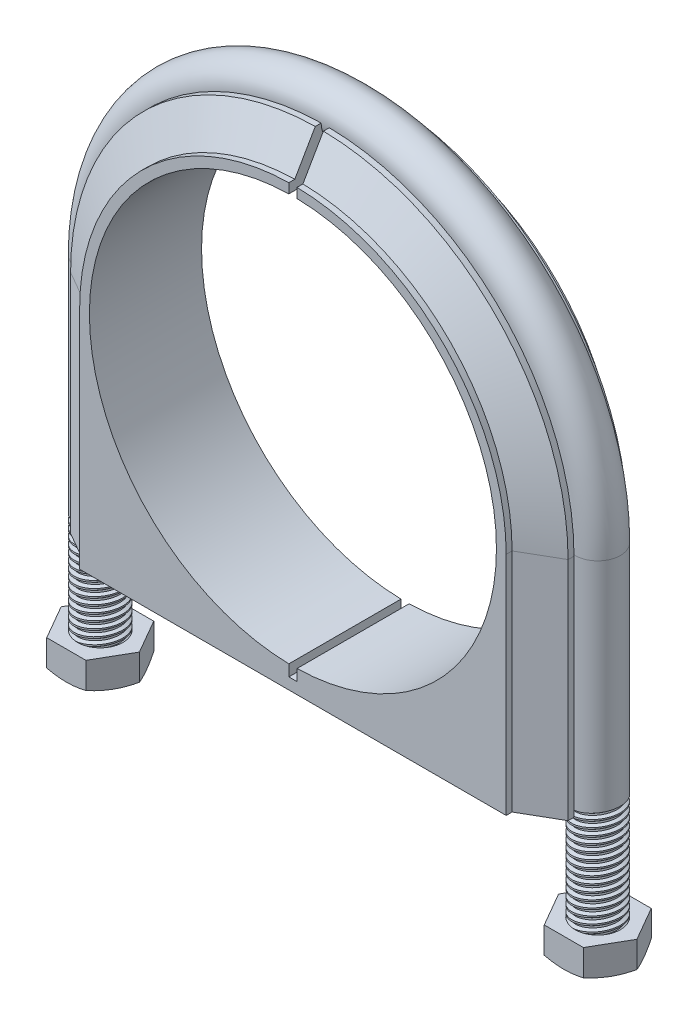
SolidWorks part; units mm, degrees
ref_plane "Front" through (0, 0, 0) normal (0, 0, 1) x (1, 0, 0)
ref_plane "Top" through (0, 0, 0) normal (0, 1, 0) x (1, 0, 0)
ref_plane "Right" through (0, 0, 0) normal (1, 0, 0) x (0, 0, -1)
sketch "Sketch1" plane through (0, 0, 0) normal (0, 0, 1) x (1, 0, 0)
  line L0 (-63.5, 0) -> (-63.5, 99.06)
  line L1 (63.5, 99.06) -> (63.5, 0)
  line L2 (-63.5, 0) -> (63.5, 0) construction
  line L3 (0, 0) -> (0, 99.06) construction
  line L4 (-69.85, 0) -> (-69.85, 99.06) construction
  line L5 (69.85, 99.06) -> (69.85, 0) construction
  line L6 (-63.5, 0) -> (-76.2, 0) construction
  line L7 (-76.2, 0) -> (-76.2, 99.06) construction
  arc A0 (-63.5, 99.06) -> (63.5, 99.06) centre (0, 99.06) cw
  arc A1 (-69.85, 99.06) -> (69.85, 99.06) centre (0, 99.06) cw construction
  dimension "ID" = 127
  dimension "Wire Dia" = 12.7
  dimension "C-C" = 139.7
  dimension "D" = 99.06
sketch "Sketch2" plane through (0, 0, 0) normal (0, 1, 0) x (1, 0, 0)
  line L0 (-63.5, 0) -> (-76.2, 0) construction
  circle A0 centre (-69.85, 0) radius 6.35
sweep "Sweep1" add profiles "Sketch2" path "Sketch1"
sketch "Sketch4" plane through (0, 0, 0) normal (0, 0, 1) x (1, 0, 0)
  line L0 (-76.2, 38.1) -> (-63.5, 38.1) construction
  line L1 (-63.5, 38.1) -> (-76.2, 36.1462) construction
  line L2 (-76.2, 36.1462) -> (-76.2, 38.1) construction
  line L3 (-63.5, 38.1) -> (-64.4524, 37.3357)
  line L4 (-64.4524, 37.3357) -> (-64.3781, 36.8529)
  line L5 (-64.3781, 36.8529) -> (-63.24, 36.4103)
  line L6 (-63.24, 36.4103) -> (-63.5, 38.1)
  line L7 (-63.24, 36.4103) -> (-63.2029, 36.1689) construction
  line L8 (-64.4153, 37.0943) -> (-63.37, 37.2551) construction
  line L9 (-76.2, 0) -> (-76.2, 99.06) construction
  line L15 (-63.5, 0) -> (-63.5, 99.06) construction
  line L16 (-63.5, 37.2351) -> (-76.2, 35.2813) construction
  line L17 (-69.5666, 34.4164) -> (-70.1334, 38.1) construction
  line L18 (-63.5, 0) -> (-76.2, 0) construction
  point P17 (-69.85, 36.2582)
  dimension "D1" = 60
  dimension "D2" = 0.2442
  dimension "D3" = 0.4885
  dimension "Thread Pitch" = 1.9538
  dimension "D4" = 1.9538
  dimension "Thread Length" = 38.1
revolve "Cut-Revolve1" cut sketch "Sketch4" angle 360 about L17
sketch "Sketch5" plane through (0, 0, 0) normal (0, 0, 1) x (1, 0, 0)
  line L0 (-63.5, 0) -> (-63.5, 2.0425)
  line L1 (-63.5, 2.0425) -> (-64.4524, 0)
  line L2 (-64.4524, 0) -> (-63.5, 0)
  line L3 (-63.5, 0) -> (-76.2, 0) construction
  line L4 (-63.5, 0) -> (-63.5, 99.06) construction
  line L5 (-69.85, -0.74) -> (-69.85, 2.2885) construction
  line L6 (-69.85, 0) -> (-69.85, 99.06) construction
  line L7 (63.5, 2.0425) -> (63.5, 0) construction
  line L8 (63.5, 0) -> (64.4524, 0) construction
  line L9 (64.4524, 0) -> (63.5, 2.0425) construction
  line L10 (63.5, 99.06) -> (63.5, 0) construction
  dimension "D1" = 25
revolve "Cut-Revolve2" cut sketch "Sketch5" angle 360 about L5
sketch "Sketch6" plane through (0, 0, 0) normal (0, 0, 1) x (1, 0, 0)
  line L0 (63.5, 0) -> (64.4524, 0) construction
  line L1 (64.4524, 0) -> (63.5, 2.0425) construction
  line L2 (63.5, 2.0425) -> (63.5, 0) construction
  line L3 (63.5, 0) -> (64.4524, 0)
  line L4 (64.4524, 0) -> (63.5, 2.0425)
  line L5 (63.5, 2.0425) -> (63.5, 0)
  line L6 (69.85, 2.7026) -> (69.85, -1.5063) construction
  line L7 (69.85, 99.06) -> (69.85, 0) construction
revolve "Cut-Revolve3" cut sketch "Sketch6" angle 360 about L6
pattern_linear "LPattern2" count 2 spacing 139.7 along (1, 0, 0) count 19 spacing 1.9538 along (0, -1, 0) of "Cut-Revolve1"
sketch "Sketch9" plane through (0, 0, 0) normal (0, 0, 1) x (1, 0, 0)
  line L0 (-63.5, 0) -> (63.5, 0) construction
  line L1 (0, 0) -> (0, 99.06) construction
  line L2 (63.5, 99.06) -> (63.5, 0) construction
  line L3 (-63.5, 0) -> (-63.5, 99.06) construction
  line L4 (-63.5, 0) -> (63.5, 0) construction
  line L5 (0, 0) -> (0, 99.06) construction
  line L6 (63.5, 99.06) -> (63.5, 35.56)
  line L7 (-63.5, 35.56) -> (-63.5, 99.06)
  line L8 (-63.5, 35.56) -> (63.5, 35.56) construction
  arc A0 (63.5, 99.06) -> (-63.5, 99.06) centre (0, 99.06) ccw construction
  arc A1 (63.5, 99.06) -> (-63.5, 99.06) centre (0, 99.06) ccw
  dimension "E" = 63.5
ref_plane "Plane2" through (0, 35.56, 0) normal (0, 1, 0) x (-1, 0, 0)
sketch "Sketch10" plane through (0, 35.56, 0) normal (0, 1, 0) x (-1, 0, 0)
  line L0 (69.85, 6.6675) -> (69.85, 8.3303)
  line L1 (69.85, 8.3303) -> (59.8823, 14.0852)
  line L2 (59.8823, 14.0852) -> (59.8823, 15.748)
  line L3 (59.8823, 15.748) -> (3.175, 15.748)
  line L4 (3.175, 15.748) -> (3.175, -15.748)
  line L5 (3.175, -15.748) -> (59.8823, -15.748)
  line L6 (59.8823, -15.748) -> (59.8823, -14.0852)
  line L7 (59.8823, -14.0852) -> (69.85, -8.3303)
  line L8 (69.85, -8.3303) -> (69.85, -6.6675)
  line L9 (76.2, 0) -> (63.5, 0) construction
  line L10 (57.15, 15.748) -> (57.15, -15.748) construction
  line L11 (0, 0) -> (0, -15.748) construction
  circle A0 centre (69.85, 0) radius 6.35 construction
  circle A1 centre (69.85, 0) radius 6.35 construction
  arc A2 (69.85, 6.6675) -> (69.85, -6.6675) centre (69.85, 0) ccw
  dimension "D1" = 12.7
  dimension "D2" = 13.335
  dimension "D3" = 30
  dimension "D4" = 3.175
  dimension "D5" = 12.7
  dimension "F" = 31.496
  dimension "A Hole" = 114.3
  dimension "D6" = 2.7323
sweep "Sweep2" add profiles "Sketch10" path "Sketch9"
sketch "Sketch11" plane through (0, 0, 0) normal (0, 0, 1) x (1, 0, 0)
  line L0 (3.175, 35.56) -> (-3.175, 35.56)
  line L6 (-59.8823, 35.56) -> (-3.175, 35.56)
  line L7 (-59.8823, 99.06) -> (-59.8823, 35.56)
  line L8 (59.8823, 35.56) -> (59.8823, 99.06)
  line L10 (3.175, 99.06) -> (3.175, 35.56)
  line L11 (-3.175, 35.56) -> (-3.175, 99.06)
  line L13 (3.175, 35.56) -> (59.8823, 35.56)
  line L16 (3.175, 99.06) -> (3.175, 35.56)
  line L17 (-3.175, 35.56) -> (-3.175, 99.06)
  arc A2 (59.8823, 99.06) -> (-59.8823, 99.06) centre (0, 99.06) ccw
  arc A3 (3.175, 99.06) -> (-3.175, 99.06) centre (0, 99.06) ccw
  arc A5 (3.175, 99.06) -> (-3.175, 99.06) centre (0, 99.06) ccw
  dimension "D1" = 0
extrude "Extrude2" add sketch "Sketch11" against normal up to surface (15.748 mm away) and the other way up to surface (15.748 mm away)
sketch "Sketch12" plane through (0, 0, 0) normal (0, 0, 1) x (1, 0, 0)
  line L0 (-57.15, 99.06) -> (57.15, 99.06) construction
  line L1 (0, 99.06) -> (0, 168.91) construction
  line L2 (-1.143, 168.91) -> (1.143, 168.91)
  line L3 (-1.143, 168.91) -> (-1.143, 156.1986)
  line L4 (-1.143, 41.9214) -> (-1.143, 38.7407)
  line L5 (1.143, 168.91) -> (1.143, 156.1986)
  line L6 (-1.143, 38.7407) -> (1.143, 38.7407)
  line L7 (1.143, 38.7407) -> (1.143, 41.9214)
  line L8 (0, 38.7407) -> (0, 35.56) construction
  arc A0 (-1.143, 156.1986) -> (-1.143, 41.9214) centre (0, 99.06) ccw
  arc A1 (63.5, 99.06) -> (-63.5, 99.06) centre (0, 99.06) ccw construction
  arc A2 (69.85, 99.06) -> (-69.85, 99.06) centre (0, 99.06) ccw construction
  arc A3 (1.143, 41.9214) -> (1.143, 156.1986) centre (0, 99.06) ccw
  dimension "D1" = 114.3
  dimension "D2" = 2.286
extrude "Cut-Extrude1" cut sketch "Sketch12" against normal through all and the other way through all
ref_plane "Plane1" through (0, 34.798, 0) normal (0, -1, 0) x (1, 0, 0)
sketch "Sketch7" plane through (0, 34.798, 0) normal (0, -1, 0) x (1, 0, 0)
  line L1 (-58.8515, 0) -> (-64.3507, 9.525)
  line L2 (-64.3507, 9.525) -> (-75.3493, 9.525)
  line L3 (-75.3493, 9.525) -> (-80.8485, 0)
  line L4 (-80.8485, 0) -> (-75.3493, -9.525)
  line L5 (-75.3493, -9.525) -> (-64.3507, -9.525)
  line L6 (-64.3507, -9.525) -> (-58.8515, 0)
  circle A0 centre (-69.85, 0) radius 6.36
  circle A1 centre (-69.85, 0) radius 9.525 construction
  dimension "D1" = 12.72
  dimension "Nut Width" = 19.05
extrude "Extrude1" add sketch "Sketch7" along normal up to surface (34.798 mm away) separate body up to face at (-69.85, 0, -5.3976)
sketch "Sketch8" plane through (0, 0, 0) normal (0, 0, 1) x (1, 0, 0)
  line L0 (-60.325, 34.798) -> (-58.8515, 34.1109)
  line L1 (-58.8515, 34.1109) -> (-58.8515, 0.6871) construction
  line L2 (-58.8515, 0.6871) -> (-60.325, 0)
  line L3 (-60.325, 0) -> (-80.8485, 0) construction
  line L4 (-80.8485, 0) -> (-80.8485, 34.798) construction
  line L5 (-80.8485, 34.798) -> (-60.325, 34.798) construction
  line L6 (-75.3493, 34.798) -> (-80.8485, 34.798) construction
  line L7 (-75.3493, 0) -> (-80.8485, 0) construction
  line L8 (-69.85, 13.5515) -> (-69.85, 10.9005) construction
  line L9 (-58.8515, 0) -> (-58.8515, 34.798) construction
  line L10 (-60.325, 34.798) -> (-58.8515, 34.798)
  line L11 (-69.85, 0) -> (-69.85, 34.798) construction
  line L12 (-58.8515, 34.798) -> (-58.8515, 34.1109)
  line L13 (-60.325, 0) -> (-58.8515, 0)
  line L14 (-58.8515, 0) -> (-58.8515, 0.6871)
  line L15 (-80.8485, 0) -> (-80.8485, 34.798) construction
  line L16 (-58.8515, 17.399) -> (-80.8485, 17.399) construction
  dimension "D1" = 25
  dimension "D2" = 19.05
revolve "Cut-Revolve4" cut sketch "Sketch8" angle 360 about L8
chamfer "Chamfer1" distance 0.1954 angle 45 2 edges at (-69.85, 0, 6.36) (-63.49, 34.798, 0)
sketch "Sketch13" plane through (0, 35.56, 0) normal (0, -1, 0) x (1, 0, 0)
  line L0 (-64.3507, 9.525) -> (-69.85, 9.525) construction
  line L1 (-69.85, 9.525) -> (-75.3493, 9.525) construction
  line L2 (-75.3493, 9.525) -> (-78.0989, 4.7625) construction
  line L3 (-78.0989, 4.7625) -> (-80.8485, 0) construction
  line L4 (-80.8485, 0) -> (-78.0989, -4.7625) construction
  line L5 (-78.0989, -4.7625) -> (-75.3493, -9.525) construction
  line L6 (-75.3493, -9.525) -> (-69.85, -9.525) construction
  line L7 (-69.85, -9.525) -> (-64.3507, -9.525) construction
  line L8 (-64.3507, -9.525) -> (-61.6011, -4.7625) construction
  line L9 (-61.6011, -4.7625) -> (-58.8515, 0) construction
  line L10 (-58.8515, 0) -> (-61.6011, 4.7625) construction
  line L11 (-61.6011, 4.7625) -> (-64.3507, 9.525) construction
  line L12 (-64.3507, 9.525) -> (-69.85, 9.525)
  line L13 (-69.85, 9.525) -> (-75.3493, 9.525)
  line L14 (-75.3493, 9.525) -> (-78.0989, 4.7625)
  line L15 (-78.0989, 4.7625) -> (-80.8485, 0)
  line L16 (-80.8485, 0) -> (-78.0989, -4.7625)
  line L17 (-78.0989, -4.7625) -> (-75.3493, -9.525)
  line L18 (-75.3493, -9.525) -> (-69.85, -9.525)
  line L19 (-69.85, -9.525) -> (-64.3507, -9.525)
  line L20 (-64.3507, -9.525) -> (-61.6011, -4.7625)
  line L21 (-61.6011, -4.7625) -> (-58.8515, 0)
  line L22 (-58.8515, 0) -> (-61.6011, 4.7625)
  line L23 (-61.6011, 4.7625) -> (-64.3507, 9.525)
  circle A1 centre (-69.85, 0) radius 6.36 construction
  circle A2 centre (-69.85, 0) radius 6.36
extrude "Cut-Extrude2" cut sketch "Sketch13" along normal blind 27.5
pattern_linear "LPattern3" count 2 spacing 139.7 along (1, 0, 0) of bodies 124 113
equation "\"D3@Sketch4\"=\"Thread Pitch@Sketch4\"/4"
equation "\"D2@Sketch4\"=\"Thread Pitch@Sketch4\"/8"
equation "\"D4@Sketch4\"=\"Thread Pitch@Sketch4\""
equation "\"D3@LPattern2\"=\"C-C@Sketch1\""
equation "\"D4@LPattern2\"=\"Thread Pitch@Sketch4\""
equation "\"D2@LPattern2\"=\"Thread Length@Sketch4\"/\"Thread Pitch@Sketch4\""
equation "\"D1@Sketch7\"=.002+\"Wire Dia@Sketch1\""
equation "\"D2@Sketch8\"=\"Nut Width@Sketch7\""
equation "\"D1@Chamfer1\"=\"Thread Pitch@Sketch4\"/10"
equation "\"D3@LPattern3\"=\"C-C@Sketch1\""
equation "\"D2@Sketch10\"=\"D1@Sketch10\"*1.05"
equation "\"D5@Sketch10\"=\"D6@Sketch10\"*2"
equation "\"D1@Sketch12\"=\"A Hole@Sketch10\""
equation "\"D2@Sketch12\"=\"D1@Sketch12\"/50"
